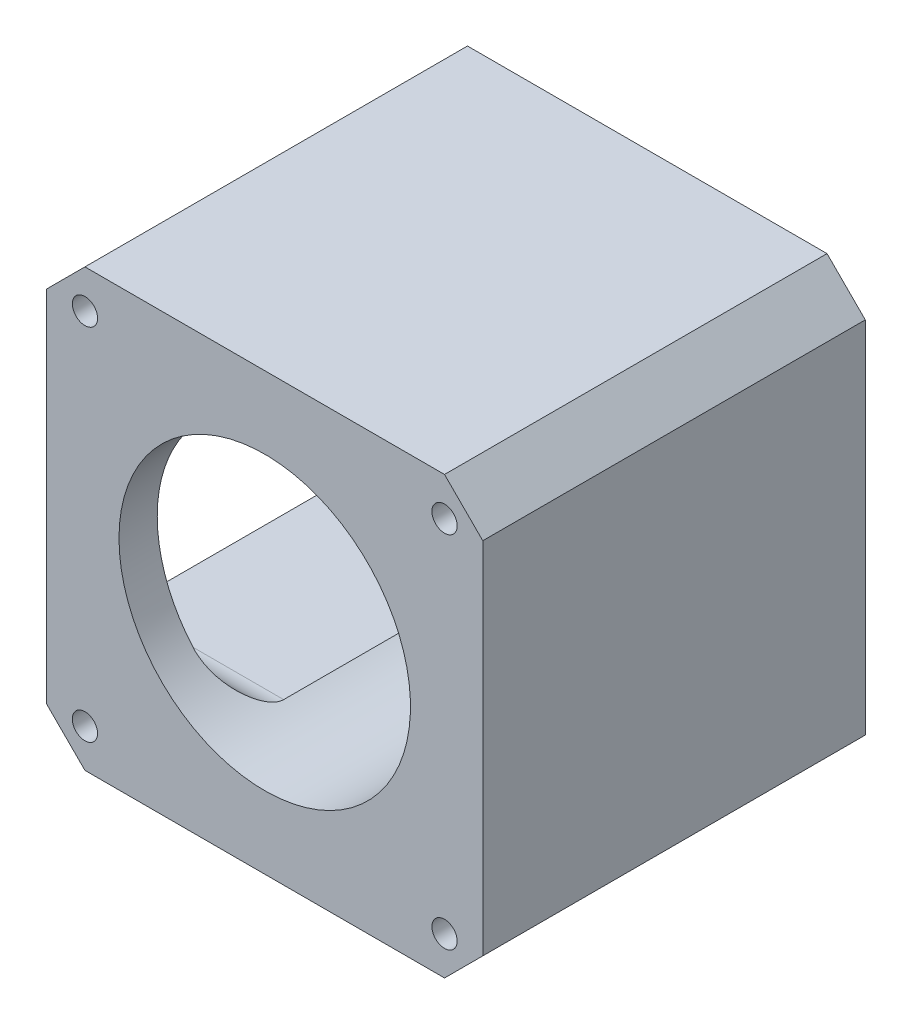
SolidWorks part; units mm, degrees
material "6061 合金"
ref_plane "前视基准面" through (0, 0, 0) normal (0, 0, 1) x (1, 0, 0)
ref_plane "上视基准面" through (0, 0, 0) normal (0, 1, 0) x (1, 0, 0)
ref_plane "右视基准面" through (0, 0, 0) normal (1, 0, 0) x (0, 0, -1)
sketch "草图1" plane through (0, 0, 0) normal (0, 0, 1) x (1, 0, 0)
  line L1 (-28.5, -28.5) -> (28.5, -28.5)
  line L2 (-28.5, -28.5) -> (-28.5, 28.5)
  line L3 (-28.5, 28.5) -> (28.5, 28.5)
  line L4 (28.5, -28.5) -> (28.5, 28.5)
  line L5 (-28.5, -28.5) -> (28.5, 28.5) construction
  line L6 (-28.5, 28.5) -> (28.5, -28.5) construction
  point P0 (0, 0)
  dimension "D1" = 57
  dimension "D2" = 57
extrude "凸台-拉伸1" add sketch "草图1" along normal mid plane 50
sketch "草图2" plane through (0, 0, -25) normal (0, 0, -1) x (-1, 0, 0)
  circle A0 centre (0, 0) radius 19.05
  dimension "D1" = 38.1
extrude "切除-拉伸1" cut sketch "草图2" against normal through all
sketch "草图3" plane through (-28.5, 0, 0) normal (1, 0, 0) x (0, 0, -1)
  line L1 (-20, -17.5) -> (20, -17.5)
  line L2 (-20, -17.5) -> (-20, 17.5)
  line L3 (-20, 17.5) -> (20, 17.5)
  line L4 (20, -17.5) -> (20, 17.5)
  line L5 (-20, -17.5) -> (20, 17.5) construction
  line L6 (-20, 17.5) -> (20, -17.5) construction
  point P0 (0, 0)
  dimension "D1" = 40
  dimension "D2" = 35
extrude "切除-拉伸2" cut sketch "草图3" along normal blind 32
chamfer "倒角1" distance 5 angle 45 4 edges at (-28.5, -28.5, 0) (-28.5, 28.5, 0) (28.5, -28.5, 0) (28.5, 28.5, 0)
hole_wizard "M4 螺纹孔1" positions "草图6" profile "草图5" tap size "M4" standard "GB"
sketch "草图6" plane through (0, 0, -25) normal (0, 0, -1) x (-1, 0, 0)
  line L0 (0, 19.05) -> (0, -38.2354) construction
  line L2 (-19.05, 0) -> (52.0653, 0) construction
  circle A0 centre (0, 0) radius 19.05 construction
  point P0 (-23.5, 23.5)
  point P3 (23.5, 23.5)
  point P6 (23.5, -23.5)
  point P9 (-23.5, -23.5)
  dimension "D1" = 47
  dimension "D2" = 47
cosmetic thread "孔螺蚊线1" parameters "D1"=12, "D2"=4
cosmetic thread "孔螺蚊线2" parameters "D1"=12, "D2"=4
cosmetic thread "孔螺蚊线3" parameters "D1"=12, "D2"=4
cosmetic thread "孔螺蚊线4" parameters "D1"=12, "D2"=4
sketch "草图5" plane through (23.5, 23.5, -25) normal (1, 0, 0) x (0, 1, 0)
  line L0 (0, 0) -> (0, 19.4914)
  line L1 (0, 19.4914) -> (1.65, 18.5)
  line L2 (1.65, 18.5) -> (1.65, 0)
  line L5 (1.65, 0) -> (0, 0)
  line L10 (0, 19.4914) -> (-1.65, 18.5) construction
  line L11 (0, -6.35) -> (0, 107.95) construction
  dimension "螺纹孔钻头直径" = 3.3
  dimension "螺纹孔钻头深度" = 18.5
  dimension "导头角度" = 118
fillet "圆角1" radius 5 4 edges at (-18.0134, -17.5, -20) (-18.0134, -17.5, 20) (-18.0134, 17.5, 20) (-18.0134, 17.5, -20)
hole_wizard "M3 螺纹孔1" positions "草图10" profile "草图9" tap size "M3" standard "GB"
sketch "草图10" plane through (-28.5, 0, 0) normal (-1, 0, 0) x (0, 0, 1)
  line L0 (-25, 0) -> (44.2534, 0) construction
  line L1 (-25, 23.5) -> (-25, -23.5) construction
  line L3 (0, 0) -> (0, 45.7509) construction
  point P0 (21, 19)
  point P2 (-21, 19)
  point P4 (-21, -19)
  point P6 (21, -19)
  dimension "D1" = 42
  dimension "D2" = 38
cosmetic thread "孔螺蚊线5" parameters "D1"=8, "D2"=3
cosmetic thread "孔螺蚊线6" parameters "D1"=8, "D2"=3
cosmetic thread "孔螺蚊线7" parameters "D1"=8, "D2"=3
cosmetic thread "孔螺蚊线8" parameters "D1"=8, "D2"=3
sketch "草图9" plane through (-28.5, 19, 21) normal (0, 1, 0) x (0, 0, 1)
  line L0 (0, 0) -> (0, 10.7511)
  line L1 (0, 10.7511) -> (1.25, 10)
  line L2 (1.25, 10) -> (1.25, 0)
  line L5 (1.25, 0) -> (0, 0)
  line L10 (0, 10.7511) -> (-1.25, 10) construction
  line L11 (0, -6.35) -> (0, 107.95) construction
  dimension "螺纹孔钻头直径" = 2.5
  dimension "螺纹孔钻头深度" = 10
  dimension "导头角度" = 118
hole_wizard "M4 螺纹孔2" positions "草图12" profile "草图11" tap size "M4" standard "GB"
sketch "草图12" plane through (0, 0, 25) normal (0, 0, 1) x (1, 0, 0)
  point P0 (23.5, 23.5)
  point P2 (-23.5, 23.5)
  point P4 (-23.5, -23.5)
  point P6 (23.5, -23.5)
sketch "草图11" plane through (23.5, 23.5, 25) normal (1, 0, 0) x (0, -1, 0)
  line L0 (0, 0) -> (0, 19.4914)
  line L1 (0, 19.4914) -> (1.65, 18.5)
  line L2 (1.65, 18.5) -> (1.65, 0)
  line L5 (1.65, 0) -> (0, 0)
  line L10 (0, 19.4914) -> (-1.65, 18.5) construction
  line L11 (0, -6.35) -> (0, 107.95) construction
  dimension "螺纹孔钻头直径" = 3.3
  dimension "螺纹孔钻头深度" = 18.5
  dimension "导头角度" = 118
cosmetic thread "孔螺蚊线9" parameters "D1"=12, "D2"=4
cosmetic thread "孔螺蚊线10" parameters "D1"=12, "D2"=4
cosmetic thread "孔螺蚊线11" parameters "D1"=12, "D2"=4
cosmetic thread "孔螺蚊线12" parameters "D1"=12, "D2"=4
